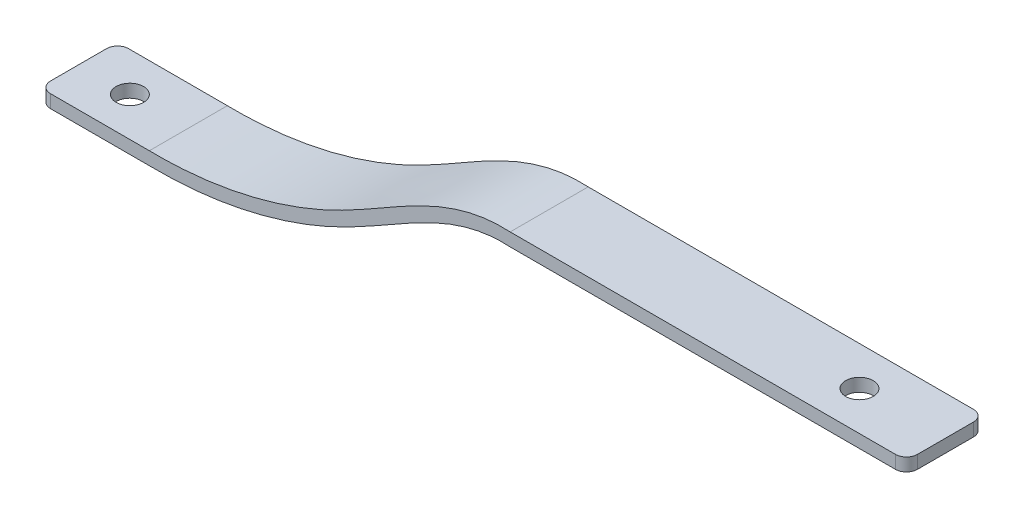
SolidWorks part; units mm, degrees
ref_plane "Front Plane" through (0, 0, 0) normal (0, 0, 1) x (1, 0, 0)
ref_plane "Top Plane" through (0, 0, 0) normal (0, 1, 0) x (1, 0, 0)
ref_plane "Right Plane" through (0, 0, 0) normal (1, 0, 0) x (0, 0, -1)
sketch "Sketch1" plane through (0, 0, 0) normal (0, 0, 1) x (1, 0, 0)
  line L0 (0, 0) -> (200, 0) construction
  line L1 (0, -25.4) -> (200, -25.4) construction
  line L2 (0, -25.4) -> (25.3267, -25.4) construction
  line L3 (108.5345, 0) -> (200, 0) construction
  line L4 (0, -26.9) -> (25.3147, -26.9)
  line L5 (108.4913, -1.5) -> (200, -1.5)
  line L6 (0, -23.9) -> (25.3389, -23.9)
  line L7 (108.5771, 1.5) -> (200, 1.5)
  line L8 (0, -23.9) -> (0, -26.9)
  line L9 (200, 1.5) -> (200, -1.5)
  spline S0 degree 3 poles (25.3267, -25.4) (40.7745, -25.6499) (69.9414, -19.0483) (94.6082, 0.8027) (108.5345, 0) knots 0 0 0 0 0.529133 1 1 1 1 construction
  spline S1 degree 1 poles (25.3147, -26.9) (108.4913, -1.5) knots 0 0 1 1 construction
  spline S2 degree 3 poles (25.3147, -26.9) (29.0188, -26.9595) (36.4383, -26.6538) (47.4523, -24.9249) (58.2625, -21.9243) (67.016, -18.3797) (73.8117, -14.8903) (80.4274, -11.1303) (86.8972, -7.3691) (93.3864, -4.327) (98.2985, -2.5787) (102.4709, -1.7035) (105.8709, -1.4283) (107.6236, -1.45) (108.4913, -1.5) knots 0.000137 0.000137 0.000137 0.000137 0.125181 0.250224 0.375268 0.500311 0.562833 0.625355 0.750399 0.812921 0.875442 0.937964 0.969225 1.000486 1.000486 1.000486 1.000486
  spline S3 degree 1 poles (25.3389, -23.9) (108.5771, 1.5) knots 0 0 1 1 construction
  spline S4 degree 3 poles (25.3389, -23.9) (28.9262, -23.958) (36.1118, -23.6648) (46.7783, -21.9941) (57.2484, -19.0934) (65.7325, -15.6625) (72.3148, -12.2885) (78.8488, -8.5791) (85.395, -4.7667) (92.1559, -1.5851) (97.3881, 0.2901) (101.9324, 1.2577) (105.6799, 1.5702) (107.6182, 1.5539) (108.5771, 1.5) knots -0.000139 -0.000139 -0.000139 -0.000139 0.12482 0.249779 0.374738 0.499697 0.562176 0.624655 0.749614 0.812094 0.874573 0.937052 0.968292 0.999532 0.999532 0.999532 0.999532
  point P3 (0, -25.4)
  point P6 (28.4213, -25.4)
  point P8 (105.1544, 0)
  point P11 (108.5345, 0)
  point P13 (25.3267, -25.4)
  point P20 (70.3809, -14.9541)
  dimension "D1" = 200
  dimension "D4" = 25.4
  dimension "D2" = 1.5
  dimension "D3" = 1.5
extrude "Boss-Extrude1" add sketch "Sketch1" along normal blind 18
sketch "Sketch2" plane through (0, 1.5, 0) normal (0, 1, 0) x (1, 0, 0)
  line L0 (0, 0) -> (0, -9) construction
  line L1 (0, -18) -> (0, 0) construction
  line L2 (0, -9) -> (200, -9) construction
  line L3 (200, -18) -> (200, 0) construction
  circle A0 centre (11.8474, -9) radius 3.175
  circle A1 centre (180.1574, -9) radius 3.175
  dimension "D1" = 6.35
  dimension "D2" = 6.35
extrude "Cut-Extrude1" cut sketch "Sketch2" against normal through all both
fillet "Fillet1" radius 2.54 4 edges at (0, -25.4, 18) (0, -25.4, 0) (200, 0, 0) (200, 0, 18)
